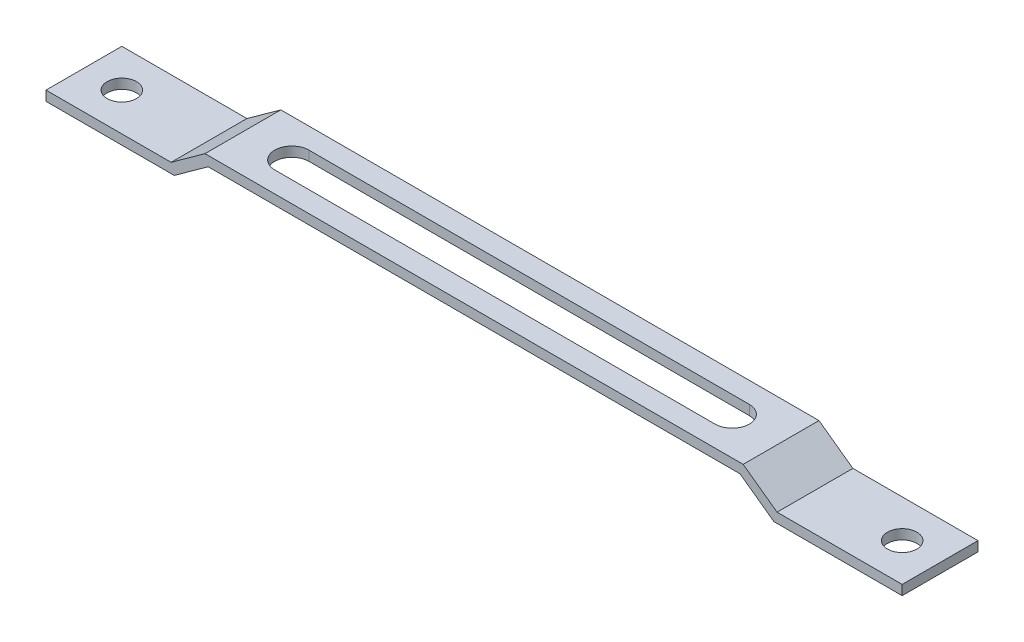
SolidWorks part; units mm, degrees
ref_plane "Спереди" through (0, 0, 0) normal (0, 0, 1) x (1, 0, 0)
ref_plane "Сверху" through (0, 0, 0) normal (0, 1, 0) x (1, 0, 0)
ref_plane "Справа" through (0, 0, 0) normal (1, 0, 0) x (0, 0, -1)
sketch "Эскиз1" plane through (0, 0, 0) normal (0, 0, 1) x (1, 0, 0)
  line L0 (55, 5) -> (-55, 5)
  line L1 (-55, 5) -> (-61.9282, 0)
  line L2 (-61.9282, 0) -> (-87.5, 0)
  line L3 (0, 38.2597) -> (0, -28.8042) construction
  line L4 (61.9282, 0) -> (87.5, 0)
  line L5 (55, 5) -> (61.9282, 0)
  point P0 (0, 0)
  point P10 (0, 5)
extrude "Вытянуть-Тонкостенный1" add sketch "Эскиз1" along normal blind 15.5 thin thin type one direction wall 2
sketch "Эскиз2" plane through (0, 5, 0) normal (0, 1, 0) x (1, 0, 0)
  line L0 (0, 11.361) -> (0, -23.4989) construction
  line L1 (-45, -4.25) -> (45, -4.25)
  line L2 (-45, -11.25) -> (45, -11.25)
  arc A0 (-45, -11.25) -> (-45, -4.25) centre (-45, -7.75) cw
  circle A1 centre (-79.75, -7.75) radius 3
  arc A2 (45, -11.25) -> (45, -4.25) centre (45, -7.75) ccw
  circle A3 centre (79.75, -7.75) radius 3
  point P1 (0, 0)
  point P11 (0, -4.25)
  point P15 (0, -11.25)
extrude "Вырез-Вытянуть1" cut sketch "Эскиз2" against normal blind 10
